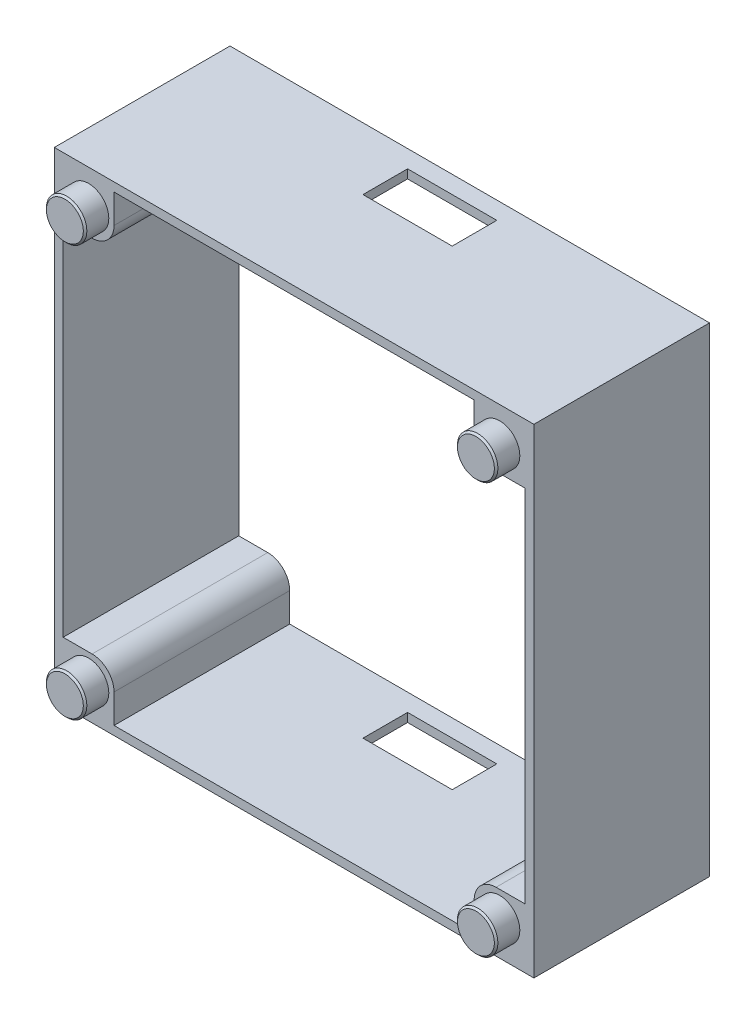
SolidWorks part; units mm, degrees
ref_plane "Přední rovina" through (0, 0, 0) normal (0, 0, 1) x (1, 0, 0)
ref_plane "Horní rovina" through (0, 0, 0) normal (0, 1, 0) x (1, 0, 0)
ref_plane "Pravá rovina" through (0, 0, 0) normal (1, 0, 0) x (0, 0, -1)
sketch "Skica1" plane through (0, 0, 0) normal (0, 0, 1) x (1, 0, 0)
  line L0 (20.5, -27.3) -> (20.5, -20.5)
  line L1 (-27.3, 27.3) -> (27.3, 27.3)
  line L2 (-27.3, 27.3) -> (-27.3, -27.3)
  line L3 (-27.3, -27.3) -> (27.3, -27.3)
  line L4 (27.3, 27.3) -> (27.3, -27.3)
  line L5 (-27.3, 27.3) -> (27.3, -27.3) construction
  line L6 (-27.3, -27.3) -> (27.3, 27.3) construction
  line L7 (-26.3, 26.3) -> (26.3, 26.3)
  line L8 (-26.3, 26.3) -> (-26.3, -26.3)
  line L9 (-26.3, -26.3) -> (26.3, -26.3)
  line L10 (26.3, 26.3) -> (26.3, -26.3)
  line L11 (-26.3, 26.3) -> (26.3, -26.3) construction
  line L12 (-26.3, -26.3) -> (26.3, 26.3) construction
  line L13 (-27.3, 27.3) -> (-20.5, 27.3)
  line L14 (-27.3, 27.3) -> (-27.3, 20.5)
  line L15 (-27.3, 20.5) -> (-20.5, 20.5)
  line L16 (-20.5, 27.3) -> (-20.5, 20.5)
  line L17 (27.3, -20.5) -> (20.5, -20.5)
  line L18 (27.3, -27.3) -> (27.3, -20.5)
  line L19 (27.3, -27.3) -> (20.5, -27.3)
  line L20 (27.3, 27.3) -> (20.5, 27.3)
  line L21 (27.3, 27.3) -> (27.3, 20.5)
  line L22 (27.3, 20.5) -> (20.5, 20.5)
  line L23 (20.5, 27.3) -> (20.5, 20.5)
  line L24 (27.3, -27.3) -> (27.3, -20.5)
  line L25 (27.3, -27.3) -> (20.5, -27.3)
  line L26 (20.5, -27.3) -> (20.5, -20.5)
  line L27 (27.3, -20.5) -> (20.5, -20.5)
  line L28 (-27.3, -27.3) -> (-20.5, -27.3)
  line L29 (-27.3, -27.3) -> (-27.3, -20.5)
  line L30 (-27.3, -20.5) -> (-20.5, -20.5)
  line L31 (-20.5, -27.3) -> (-20.5, -20.5)
  point P0 (0, 0)
  point P5 (0, 0)
  point P32 (0, 0)
  dimension "D1" = 54.6
  dimension "D2" = 52.6
  dimension "D3" = 6.8
  dimension "D4" = 4
extrude "Přidat vysunutím2" add sketch "Skica1" along normal blind 20 contours L16 L1 L2 L15 L8 L7 | L16 L7 L8 L15 | L1 L23 L7 L10 L22 L4 | L7 L23 L22 L10 | L4 L17 L10 L9 L0 L3 | L10 L17 L0 L9 | L9 L31 L30 L8 | L3 L31 L9 L8 L30 L2 | L2 L30 L8 L15 | L31 L3 L0 L9 | L4 L22 L10 L17 | L23 L1 L16 L7
fillet "Zaoblit1" radius 2.5 4 edges at (-20.5, -20.5, 10) (20.5, -20.5, 10) (20.5, 20.5, 10) (-20.5, 20.5, 10)
sketch "Skica2" plane through (0, 0, 0) normal (0, 0, -1) x (-1, 0, 0)
  line L0 (-27.3, 27.3) -> (-27.3, -27.3) construction
  line L1 (27.3, 27.3) -> (-27.3, 27.3) construction
  circle A0 centre (-23.4, 23.4) radius 2.4
  circle A1 centre (23.4, 23.4) radius 2.4
  circle A2 centre (23.4, -23.4) radius 2.4
  circle A3 centre (-23.4, -23.4) radius 2.4
  point P15 (0, 0)
  dimension "D1" = 4.8
  dimension "D2" = 3.9
  dimension "D3" = 3.9
  dimension "D4" = 4
extrude "Odebrat vysunutím1" cut sketch "Skica2" against normal blind 1.7
sketch "Skica3" plane through (0, 0, 20) normal (0, 0, 1) x (1, 0, 0)
  line L0 (-27.3, 27.3) -> (-27.3, -27.3) construction
  line L1 (-27.3, 27.3) -> (27.3, 27.3) construction
  circle A0 centre (-23.4, 23.4) radius 2.3
  circle A1 centre (23.4, 23.4) radius 2.3
  circle A2 centre (23.4, -23.4) radius 2.3
  circle A3 centre (-23.4, -23.4) radius 2.3
  point P15 (0, 0)
  dimension "D1" = 4.6
  dimension "D2" = 3.9
  dimension "D3" = 3.9
  dimension "D4" = 4
extrude "Přidat vysunutím3" add sketch "Skica3" along normal blind 2.7
chamfer "Zkosení1" distance 0.2 angle 45 4 edges at (25.7, -23.4, 22.7) (25.7, 23.4, 22.7) (-21.1, -23.4, 22.7) (-21.1, 23.4, 22.7)
sketch "Skica4" plane through (0, -27.3, 0) normal (0, -1, 0) x (-1, 0, 0)
  line L0 (27.3, -20) -> (27.3, 0) construction
  line L1 (5.08, -7.08) -> (-5.08, -7.08)
  line L2 (5.08, -7.08) -> (5.08, -2)
  line L3 (5.08, -2) -> (-5.08, -2)
  line L4 (-5.08, -7.08) -> (-5.08, -2)
  line L5 (-27.3, -20) -> (-27.3, 0) construction
  line L6 (27.3, 0) -> (-27.3, 0) construction
  dimension "D1" = 5.08
  dimension "D2" = 10.16
  dimension "D3" = 22.22
  dimension "D4" = 22.22
  dimension "D5" = 2
extrude "Odebrat vysunutím2" cut sketch "Skica4" against normal blind 68.7
